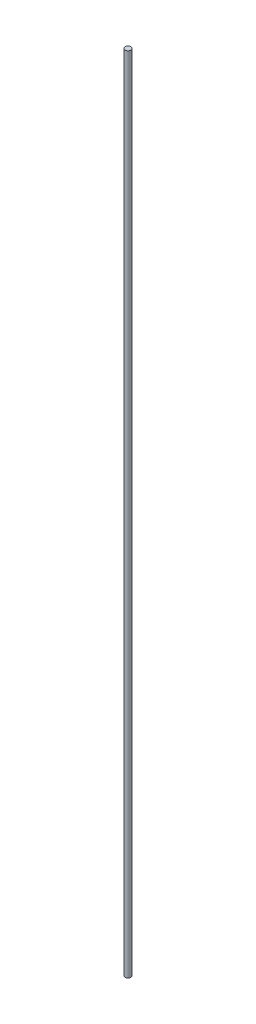
SolidWorks part; units mm, degrees
ref_plane "Front Plane" through (0, 0, 0) normal (0, 0, 1) x (1, 0, 0)
ref_plane "Top Plane" through (0, 0, 0) normal (0, 1, 0) x (1, 0, 0)
ref_plane "Right Plane" through (0, 0, 0) normal (1, 0, 0) x (0, 0, -1)
sketch "Sketch1" plane through (0, 0, 0) normal (0, 1, 0) x (1, 0, 0)
  circle A0 centre (0, 0) radius 0.5
  dimension "D1" = 1
extrude "Boss-Extrude1" add sketch "Sketch1" along normal blind 136.17
